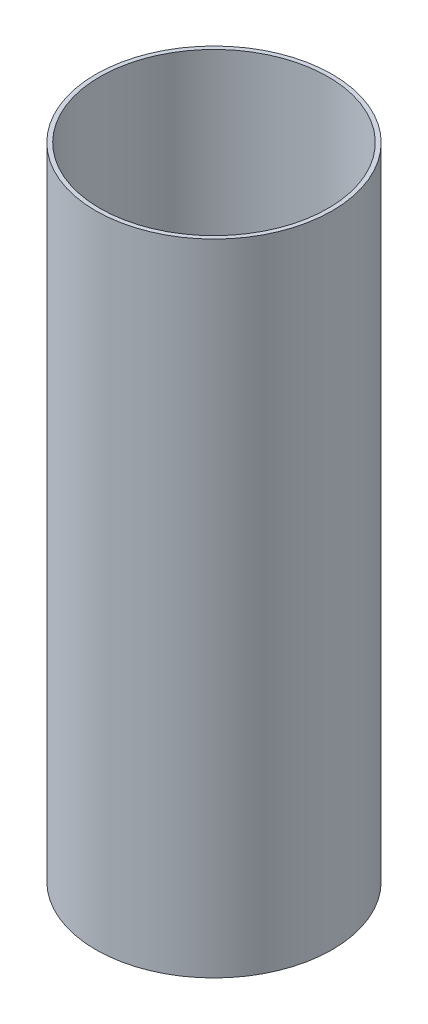
SolidWorks part; units mm, degrees
ref_plane "Front Plane" through (0, 0, 0) normal (0, 0, 1) x (1, 0, 0)
ref_plane "Top Plane" through (0, 0, 0) normal (0, 1, 0) x (1, 0, 0)
ref_plane "Right Plane" through (0, 0, 0) normal (1, 0, 0) x (0, 0, -1)
sketch "Sketch1" plane through (0, 0, 0) normal (0, 1, 0) x (1, 0, 0)
  circle A0 centre (0, 0) radius 42.5
  circle A1 centre (0, 0) radius 41
  dimension "D1" = 82
  dimension "D2" = 1.5
extrude "Boss-Extrude1" add sketch "Sketch1" along normal blind 230
